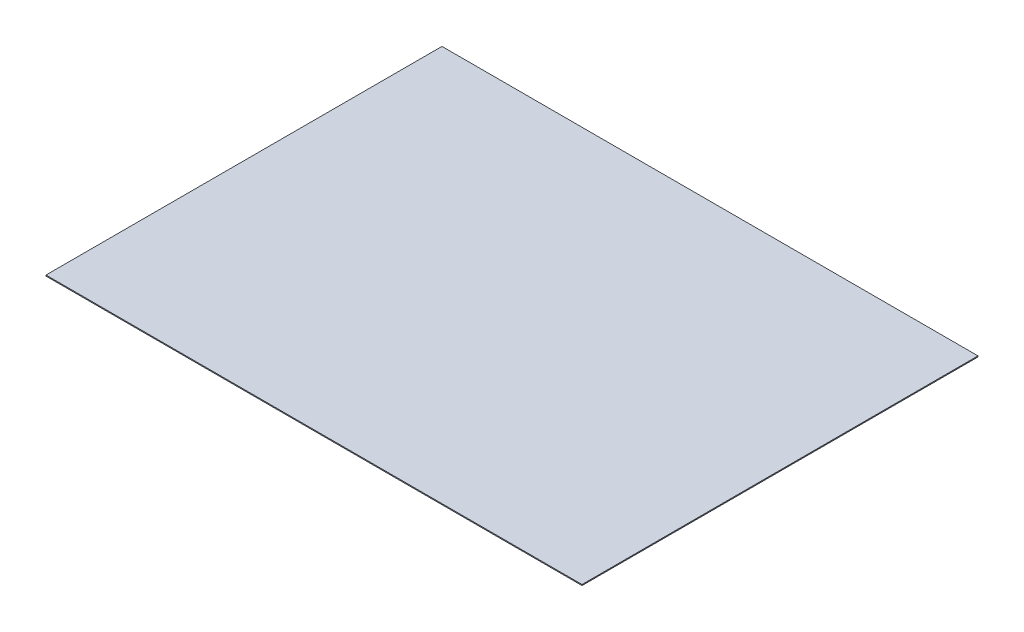
SolidWorks part; units mm, degrees
material "Pine"
ref_plane "Front Plane" through (0, 0, 0) normal (0, 0, 1) x (1, 0, 0)
ref_plane "Top Plane" through (0, 0, 0) normal (0, 1, 0) x (1, 0, 0)
ref_plane "Right Plane" through (0, 0, 0) normal (1, 0, 0) x (0, 0, -1)
sketch "Sketch1" plane through (0, 0, 0) normal (0, 1, 0) x (1, 0, 0)
  line L1 (0, 0) -> (1616.075, 0)
  line L2 (0, 0) -> (0, 1193.8)
  line L3 (0, 1193.8) -> (1616.075, 1193.8)
  line L4 (1616.075, 0) -> (1616.075, 1193.8)
  dimension "D1" = 1193.8
  dimension "D2" = 1616.075
extrude "Boss-Extrude1" add sketch "Sketch1" along normal blind 2.921
